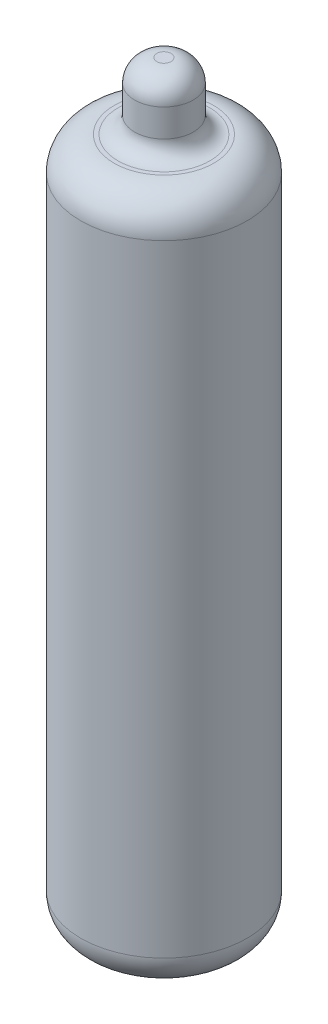
SolidWorks part; units mm, degrees
material "ABS PC"
ref_plane "Plan de face" through (0, 0, 0) normal (0, 0, 1) x (1, 0, 0)
ref_plane "Plan de dessus" through (0, 0, 0) normal (0, 1, 0) x (1, 0, 0)
ref_plane "Plan de droite" through (0, 0, 0) normal (1, 0, 0) x (0, 0, -1)
sketch "Esquisse1" plane through (0, 0, 0) normal (0, 0, 1) x (1, 0, 0)
  line L0 (0, 0) -> (0, 62) construction
  line L1 (0, 0) -> (0, 68) construction
  line L2 (0, 0) -> (7.5, 0) construction
  line L3 (0, 0) -> (4.5, 0)
  line L4 (7.5, 3) -> (7.5, 59)
  line L5 (4.5, 62) -> (4.1407, 62)
  line L6 (2.6407, 63.5) -> (2.6407, 66)
  line L7 (0.6407, 68) -> (0, 68)
  line L8 (0, 68) -> (0, 0)
  arc A0 (7.5, 59) -> (4.5, 62) centre (4.5, 59) ccw
  arc A1 (4.5, 0) -> (7.5, 3) centre (4.5, 3) ccw
  arc A2 (0.6407, 68) -> (2.6407, 66) centre (0.6407, 66) cw
  arc A3 (2.6407, 63.5) -> (4.1407, 62) centre (4.1407, 63.5) ccw
  dimension "D4" = 3
  dimension "D3" = 2
  dimension "D5" = 1.5
  dimension "D1" = 62
  dimension "D2" = 68
revolve "Révolution1" add sketch "Esquisse1" angle 360 about L8
